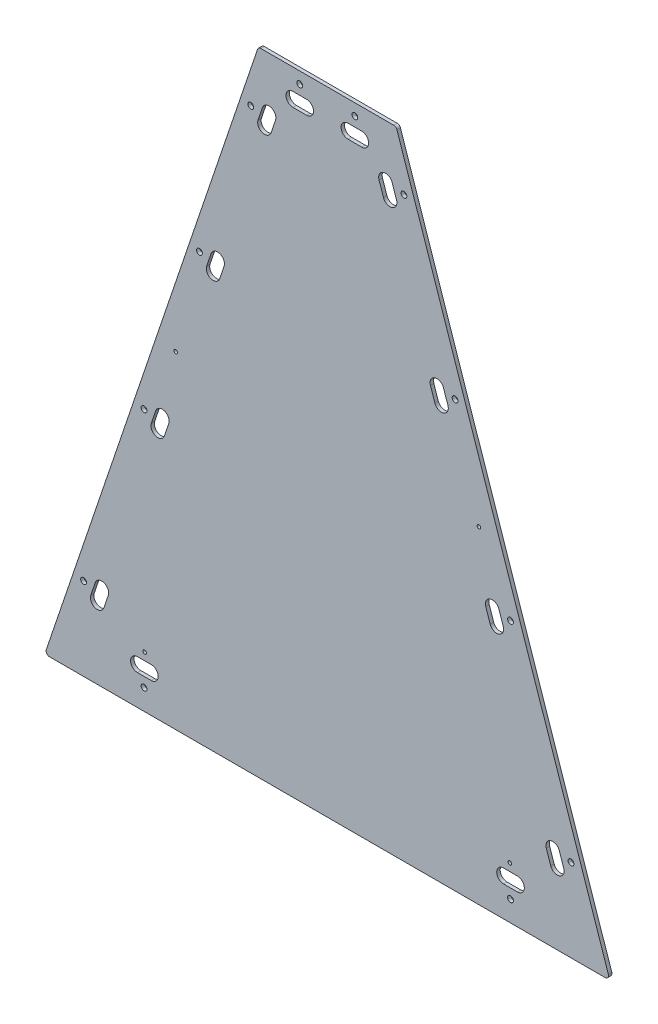
SolidWorks part; units mm, degrees
material "PC High Viscosity"
ref_plane "Front Plane" through (0, 0, 0) normal (0, 0, 1) x (1, 0, 0)
ref_plane "Top Plane" through (0, 0, 0) normal (0, 1, 0) x (1, 0, 0)
ref_plane "Right Plane" through (0, 0, 0) normal (1, 0, 0) x (0, 0, -1)
sketch "Sketch1" plane through (0, 0, 0) normal (0, 0, 1) x (1, 0, 0)
  line L0 (128.5466, 292.9716) -> (382.5466, 292.9716)
  line L5 (382.5466, 292.9716) -> (776.2466, -872.6346)
  line L6 (776.2466, -872.6346) -> (-265.1534, -872.6346)
  line L7 (-265.1534, -872.6346) -> (128.5466, 292.9716)
  line L8 (-168.2075, -740.392) -> (-160.0795, -716.3277) construction
  line L9 (-180.2397, -736.328) -> (-172.1116, -712.2636)
  line L10 (-156.1753, -744.4561) -> (-148.0473, -720.3917)
  line L11 (-94.2317, -804.0546) -> (-68.8317, -804.0546) construction
  line L12 (-94.2317, -791.3546) -> (-68.8317, -791.3546)
  line L13 (-94.2317, -816.7546) -> (-68.8317, -816.7546)
  line L14 (580.5201, -804.0546) -> (605.9201, -804.0546) construction
  line L15 (580.5201, -791.3546) -> (605.9201, -791.3546)
  line L16 (580.5201, -816.7546) -> (605.9201, -816.7546)
  line L17 (-56.7399, -410.3759) -> (-48.6118, -386.3115) construction
  line L18 (-68.7721, -406.3118) -> (-60.644, -382.2474)
  line L19 (-44.7077, -414.4399) -> (-36.5796, -390.3755)
  line L20 (45.2346, -108.4656) -> (53.3626, -84.4012) construction
  line L21 (33.2024, -104.4015) -> (41.3305, -80.3372)
  line L22 (57.2668, -112.5296) -> (65.3948, -88.4652)
  line L29 (139.9814, 172.0464) -> (148.1095, 196.1108) construction
  line L30 (127.9493, 176.1104) -> (136.0773, 200.1748)
  line L31 (152.0136, 167.9823) -> (160.1417, 192.0467)
  line L32 (192.1135, 241.2472) -> (217.5135, 241.2472) construction
  line L33 (192.1135, 253.9472) -> (217.5135, 253.9472)
  line L34 (192.1135, 228.5472) -> (217.5135, 228.5472)
  line L35 (293.6466, 241.2472) -> (319.0466, 241.2472) construction
  line L36 (293.6466, 253.9472) -> (319.0466, 253.9472)
  line L37 (293.6466, 228.5472) -> (319.0466, 228.5472)
  line L38 (371.0972, 172.0897) -> (362.9691, 196.154) construction
  line L39 (359.065, 168.0256) -> (350.9369, 192.09)
  line L40 (383.1294, 176.1537) -> (375.0013, 200.2181)
  line L41 (465.8587, -108.4656) -> (457.7306, -84.4012) construction
  line L42 (453.8265, -112.5296) -> (445.6984, -88.4652)
  line L43 (477.8909, -104.4015) -> (469.7628, -80.3372)
  line L44 (679.3008, -740.392) -> (671.1727, -716.3277) construction
  line L47 (567.8332, -410.3759) -> (559.7051, -386.3115) construction
  line L48 (555.801, -414.4399) -> (547.6729, -390.3755)
  line L49 (579.8654, -406.3118) -> (571.7373, -382.2474)
  line L50 (667.2686, -744.4561) -> (659.1405, -720.3917)
  line L53 (691.333, -736.328) -> (683.2049, -712.2636)
  circle A0 centre (396.7562, 191.3716) radius 5.3578
  circle A1 centre (114.6592, 192.3252) radius 5.3578
  circle A2 centre (-193.5708, -720.2346) radius 5.3578
  circle A4 centre (704.6641, -720.2346) radius 5.3578
  circle A5 centre (491.1275, -88.0284) radius 5.3578
  circle A6 centre (593.2201, -390.2884) radius 5.3578
  circle A7 centre (19.9658, -88.0284) radius 5.3578
  circle A8 centre (-82.1268, -390.2884) radius 5.3578
  circle A9 centre (306.3466, 271.7272) radius 5.3578
  circle A10 centre (204.7466, 271.7272) radius 5.3578
  circle A12 centre (-82.1268, -834.5346) radius 5.3578
  circle A13 centre (593.2201, -834.5346) radius 5.3578
  arc A14 (-180.2397, -736.328) -> (-156.1753, -744.4561) centre (-168.2075, -740.392) ccw
  arc A15 (-148.0473, -720.3917) -> (-172.1116, -712.2636) centre (-160.0795, -716.3277) ccw
  arc A16 (-94.2317, -791.3546) -> (-94.2317, -816.7546) centre (-94.2317, -804.0546) ccw
  arc A17 (-68.8317, -816.7546) -> (-68.8317, -791.3546) centre (-68.8317, -804.0546) ccw
  arc A18 (580.5201, -791.3546) -> (580.5201, -816.7546) centre (580.5201, -804.0546) ccw
  arc A19 (605.9201, -816.7546) -> (605.9201, -791.3546) centre (605.9201, -804.0546) ccw
  arc A20 (-68.7721, -406.3118) -> (-44.7077, -414.4399) centre (-56.7399, -410.3759) ccw
  arc A21 (-36.5796, -390.3755) -> (-60.644, -382.2474) centre (-48.6118, -386.3115) ccw
  arc A22 (33.2024, -104.4015) -> (57.2668, -112.5296) centre (45.2346, -108.4656) ccw
  arc A23 (65.3948, -88.4652) -> (41.3305, -80.3372) centre (53.3626, -84.4012) ccw
  arc A28 (127.9493, 176.1104) -> (152.0136, 167.9823) centre (139.9814, 172.0464) ccw
  arc A29 (160.1417, 192.0467) -> (136.0773, 200.1748) centre (148.1095, 196.1108) ccw
  arc A30 (192.1135, 253.9472) -> (192.1135, 228.5472) centre (192.1135, 241.2472) ccw
  arc A31 (217.5135, 228.5472) -> (217.5135, 253.9472) centre (217.5135, 241.2472) ccw
  arc A32 (293.6466, 253.9472) -> (293.6466, 228.5472) centre (293.6466, 241.2472) ccw
  arc A33 (319.0466, 228.5472) -> (319.0466, 253.9472) centre (319.0466, 241.2472) ccw
  arc A34 (359.065, 168.0256) -> (383.1294, 176.1537) centre (371.0972, 172.0897) ccw
  arc A35 (375.0013, 200.2181) -> (350.9369, 192.09) centre (362.9691, 196.154) ccw
  arc A36 (453.8265, -112.5296) -> (477.8909, -104.4015) centre (465.8587, -108.4656) ccw
  arc A37 (469.7628, -80.3372) -> (445.6984, -88.4652) centre (457.7306, -84.4012) ccw
  arc A40 (555.801, -414.4399) -> (579.8654, -406.3118) centre (567.8332, -410.3759) ccw
  arc A41 (571.7373, -382.2474) -> (547.6729, -390.3755) centre (559.7051, -386.3115) ccw
  arc A44 (667.2686, -744.4561) -> (691.333, -736.328) centre (679.3008, -740.392) ccw
  arc A45 (683.2049, -712.2636) -> (659.1405, -720.3917) centre (671.1727, -716.3277) ccw
  point P24 (-164.1435, -728.3598)
  point P39 (-81.5317, -804.0546)
  point P47 (593.2201, -804.0546)
  point P56 (-52.6759, -398.3437)
  point P62 (204.8135, 241.2472)
  point P65 (49.2986, -96.4334)
  point P93 (144.0455, 184.0786)
  point P106 (306.3466, 241.2472)
  point P115 (367.0332, 184.1219)
  point P125 (461.7947, -96.4334)
  point P136 (675.2368, -728.3598)
  point P140 (563.7691, -398.3437)
  dimension "D5" = 10.7156
  dimension "D6" = 19.05
  dimension "D7" = 17.78
  dimension "D8" = 17.78
  dimension "D9" = 17.78
  dimension "D10" = 17.78
  dimension "D11" = 17.78
  dimension "D12" = 17.78
  dimension "D13" = 38.1
  dimension "D31" = 183.6216
  dimension "D32" = 144.2748
  dimension "D36" = 108.893
  dimension "D37" = 17.78
  dimension "D41" = 76.2669
  dimension "D34" = 776.2012
  dimension "D35" = 25.4
  dimension "D1" = 254
  dimension "D2" = 1230.2998
  dimension "D3" = 1230.2998
  dimension "D4" = 1041.4
  dimension "D14" = 19.05
  dimension "D15" = 683.26
  dimension "D16" = 19.05
  dimension "D17" = 76.2
  dimension "D18" = 381
  dimension "D19" = 683.26
  dimension "D20" = 152.4
  dimension "D21" = 152.4
  dimension "D22" = 19.05
  dimension "D23" = 76.2
  dimension "D24" = 19.05
  dimension "D25" = 381
  dimension "D26" = 101.6
  dimension "D27" = 19.05
  dimension "D28" = 19.05
  dimension "D29" = 19.05
  dimension "D30" = 101.6
  dimension "D33" = 474.291
  dimension "D38" = 38.1
  dimension "D39" = 25.4
  dimension "D40" = 17.78
  dimension "D42" = 17.78
  dimension "D43" = 108.8497
  dimension "D47" = 17.78
  dimension "D52" = 17.78
  dimension "D53" = 17.78
  dimension "D56" = 21.2444
  dimension "D57" = 21.2444
extrude "Boss-Extrude1" add sketch "Sketch1" along normal blind 6.35 contours L7 L6 L5 L0 A29 L31 A28 L30 A23 L22 A22 L21 A21 L19 A20 L18 A19 L16 A18 L15 A17 L13 A16 L12 A15 L10 A14 L9 A13 A12 A10 A9 A8 A7 A6 A5
fillet "Fillet1" radius 6.35 4 edges at (-265.1534, -872.6346, 3.175) (776.2466, -872.6346, 3.175) (382.5466, 292.9716, 3.175) (128.5466, 292.9716, 3.175)
sketch "Sketch2" plane through (0, 0, 6.35) normal (0, 0, 1) x (1, 0, 0)
  line L0 (255.5466, -872.6346) -> (255.5466, 292.9716) construction
  line L1 (767.3994, -872.6346) -> (-256.3061, -872.6346) construction
  line L2 (133.1043, 292.9716) -> (377.989, 292.9716) construction
  line L3 (91.6472, -808.2573) -> (67.9728, -842.0678)
  line L4 (443.1205, -842.0678) -> (419.4461, -808.2573)
  arc A0 (91.6472, -808.2573) -> (419.4461, -808.2573) centre (255.5466, -574.1846) cw
  arc A1 (67.9728, -842.0678) -> (443.1205, -842.0678) centre (255.5466, -574.1846) cw
  point P0 (255.5466, -288.4346)
  dimension "D3" = 298.45
  dimension "D1" = 41.275
  dimension "D2" = 584.2
  dimension "D4" = 70
sketch "Sketch4" [suppressed] plane through (0, 0, 6.35) normal (0, 0, 1) x (1, 0, 0)
  line L0 (414.1087, -288.4346) -> (255.5466, -288.4346)
  line L13 (414.1087, -288.4346) -> (572.6707, -563.0721)
  line L14 (572.6707, -563.0721) -> (414.1087, -837.7096)
  line L15 (767.3994, -872.6346) -> (-256.3061, -872.6346) construction
  line L16 (255.5466, -288.4346) -> (255.5466, -872.6346) construction
  line L17 (437.9388, -247.1596) -> (255.5466, -247.1596)
  line L18 (437.9388, -247.1596) -> (620.331, -563.0721)
  line L19 (620.331, -563.0721) -> (449.8539, -858.3471)
  line L20 (449.8539, -858.3471) -> (414.1087, -837.7096)
  line L21 (61.2394, -858.3471) -> (96.9846, -837.7096)
  line L22 (-109.2377, -563.0721) -> (61.2394, -858.3471)
  line L23 (73.1545, -247.1596) -> (-109.2377, -563.0721)
  line L24 (73.1545, -247.1596) -> (255.5466, -247.1596)
  line L25 (-61.5774, -563.0721) -> (96.9846, -837.7096)
  line L26 (96.9846, -288.4346) -> (-61.5774, -563.0721)
  line L27 (96.9846, -288.4346) -> (255.5466, -288.4346)
  line L28 (414.1087, -837.7096) -> (96.9846, -837.7096) construction
  dimension "D1" = 309.5625
  dimension "D2" = 317.1241
  dimension "D3" = 120
  dimension "D4" = 120
  dimension "D5" = 41.275
extrude "Cut-Extrude1" [suppressed] cut sketch "Sketch2" against normal through all
extrude "Cut-Extrude2" [suppressed] cut sketch "Sketch4" against normal through all
sketch "Sketch5" [suppressed] plane through (0, 0, 6.35) normal (0, 0, 1) x (1, 0, 0)
  line L0 (57.2668, -112.5296) -> (65.3948, -88.4652) construction
  line L1 (33.2024, -104.4015) -> (41.3305, -80.3372) construction
  line L2 (-44.7077, -414.4399) -> (-36.5796, -390.3755) construction
  line L3 (-68.7721, -406.3118) -> (-60.644, -382.2474) construction
  line L4 (-180.2397, -736.328) -> (-172.1116, -712.2636) construction
  line L5 (-156.1753, -744.4561) -> (-148.0473, -720.3917) construction
  line L6 (-94.2317, -816.7546) -> (-68.8317, -816.7546) construction
  line L7 (-94.2317, -791.3546) -> (-68.8317, -791.3546) construction
  line L8 (57.2668, -112.5296) -> (65.3948, -88.4652)
  line L9 (33.2024, -104.4015) -> (41.3305, -80.3372)
  line L10 (-44.7077, -414.4399) -> (-36.5796, -390.3755)
  line L11 (-68.7721, -406.3118) -> (-60.644, -382.2474)
  line L12 (-180.2397, -736.328) -> (-172.1116, -712.2636)
  line L13 (-156.1753, -744.4561) -> (-148.0473, -720.3917)
  line L14 (-94.2317, -816.7546) -> (-68.8317, -816.7546)
  line L15 (-94.2317, -791.3546) -> (-68.8317, -791.3546)
  line L16 (192.1135, 228.5472) -> (217.5135, 228.5472) construction
  line L17 (192.1135, 253.9472) -> (217.5135, 253.9472) construction
  line L18 (152.0136, 167.9823) -> (160.1417, 192.0467) construction
  line L19 (127.9493, 176.1104) -> (136.0773, 200.1748) construction
  line L20 (192.1135, 228.5472) -> (217.5135, 228.5472)
  line L21 (192.1135, 253.9472) -> (217.5135, 253.9472)
  line L22 (152.0136, 167.9823) -> (160.1417, 192.0467)
  line L23 (127.9493, 176.1104) -> (136.0773, 200.1748)
  line L24 (255.5466, 292.9716) -> (255.5466, -872.6346) construction
  line L37 (359.065, 168.0256) -> (350.9369, 192.09) construction
  line L38 (383.1294, 176.1537) -> (375.0013, 200.2181) construction
  line L39 (293.6466, 228.5472) -> (319.0466, 228.5472) construction
  line L40 (293.6466, 253.9472) -> (319.0466, 253.9472) construction
  line L41 (359.065, 168.0256) -> (350.9369, 192.09)
  line L42 (383.1294, 176.1537) -> (375.0013, 200.2181)
  line L43 (293.6466, 228.5472) -> (319.0466, 228.5472)
  line L44 (293.6466, 253.9472) -> (319.0466, 253.9472)
  line L45 (453.8265, -112.5296) -> (445.6984, -88.4652) construction
  line L46 (477.8909, -104.4015) -> (469.7628, -80.3372) construction
  line L47 (453.8265, -112.5296) -> (445.6984, -88.4652)
  line L48 (477.8909, -104.4015) -> (469.7628, -80.3372)
  line L49 (555.801, -414.4399) -> (547.6729, -390.3755) construction
  line L50 (579.8654, -406.3118) -> (571.7373, -382.2474) construction
  line L51 (555.801, -414.4399) -> (547.6729, -390.3755)
  line L52 (579.8654, -406.3118) -> (571.7373, -382.2474)
  line L53 (667.2686, -744.4561) -> (659.1405, -720.3917) construction
  line L54 (691.333, -736.328) -> (683.2049, -712.2636) construction
  line L55 (667.2686, -744.4561) -> (659.1405, -720.3917)
  line L56 (691.333, -736.328) -> (683.2049, -712.2636)
  line L57 (580.5201, -791.3546) -> (605.9201, -791.3546) construction
  line L58 (580.5201, -816.7546) -> (605.9201, -816.7546) construction
  line L59 (580.5201, -791.3546) -> (605.9201, -791.3546)
  line L60 (580.5201, -816.7546) -> (605.9201, -816.7546)
  arc A0 (33.2024, -104.4015) -> (57.2668, -112.5296) centre (45.2346, -108.4656) ccw construction
  arc A1 (65.3948, -88.4652) -> (41.3305, -80.3372) centre (53.3626, -84.4012) ccw construction
  circle A2 centre (19.9658, -88.0284) radius 5.3578 construction
  arc A3 (-68.7721, -406.3118) -> (-44.7077, -414.4399) centre (-56.7399, -410.3759) ccw construction
  circle A4 centre (-82.1268, -390.2884) radius 5.3578 construction
  arc A5 (-36.5796, -390.3755) -> (-60.644, -382.2474) centre (-48.6118, -386.3115) ccw construction
  circle A6 centre (-193.5708, -720.2346) radius 5.3578 construction
  arc A7 (-148.0473, -720.3917) -> (-172.1116, -712.2636) centre (-160.0795, -716.3277) ccw construction
  arc A8 (-180.2397, -736.328) -> (-156.1753, -744.4561) centre (-168.2075, -740.392) ccw construction
  arc A9 (-94.2317, -791.3546) -> (-94.2317, -816.7546) centre (-94.2317, -804.0546) ccw construction
  arc A10 (-68.8317, -816.7546) -> (-68.8317, -791.3546) centre (-68.8317, -804.0546) ccw construction
  circle A11 centre (-82.1268, -834.5346) radius 5.3578 construction
  arc A12 (33.2024, -104.4015) -> (57.2668, -112.5296) centre (45.2346, -108.4656) ccw
  arc A13 (65.3948, -88.4652) -> (41.3305, -80.3372) centre (53.3626, -84.4012) ccw
  circle A14 centre (19.9658, -88.0284) radius 5.3578
  arc A15 (-68.7721, -406.3118) -> (-44.7077, -414.4399) centre (-56.7399, -410.3759) ccw
  circle A16 centre (-82.1268, -390.2884) radius 5.3578
  arc A17 (-36.5796, -390.3755) -> (-60.644, -382.2474) centre (-48.6118, -386.3115) ccw
  circle A18 centre (-193.5708, -720.2346) radius 5.3578
  arc A19 (-148.0473, -720.3917) -> (-172.1116, -712.2636) centre (-160.0795, -716.3277) ccw
  arc A20 (-180.2397, -736.328) -> (-156.1753, -744.4561) centre (-168.2075, -740.392) ccw
  arc A21 (-94.2317, -791.3546) -> (-94.2317, -816.7546) centre (-94.2317, -804.0546) ccw
  arc A22 (-68.8317, -816.7546) -> (-68.8317, -791.3546) centre (-68.8317, -804.0546) ccw
  circle A23 centre (-82.1268, -834.5346) radius 5.3578
  arc A24 (217.5135, 228.5472) -> (217.5135, 253.9472) centre (217.5135, 241.2472) ccw construction
  arc A25 (192.1135, 253.9472) -> (192.1135, 228.5472) centre (192.1135, 241.2472) ccw construction
  circle A26 centre (204.7466, 271.7272) radius 5.3578 construction
  arc A27 (127.9493, 176.1104) -> (152.0136, 167.9823) centre (139.9814, 172.0464) ccw construction
  arc A28 (160.1417, 192.0467) -> (136.0773, 200.1748) centre (148.1095, 196.1108) ccw construction
  circle A29 centre (114.6592, 192.3252) radius 5.3578 construction
  arc A30 (217.5135, 228.5472) -> (217.5135, 253.9472) centre (217.5135, 241.2472) ccw
  arc A31 (192.1135, 253.9472) -> (192.1135, 228.5472) centre (192.1135, 241.2472) ccw
  circle A32 centre (204.7466, 271.7272) radius 5.3578
  arc A33 (127.9493, 176.1104) -> (152.0136, 167.9823) centre (139.9814, 172.0464) ccw
  arc A34 (160.1417, 192.0467) -> (136.0773, 200.1748) centre (148.1095, 196.1108) ccw
  circle A35 centre (114.6592, 192.3252) radius 5.3578
  circle A54 centre (306.3466, 271.7272) radius 5.3578 construction
  circle A55 centre (306.3466, 271.7272) radius 5.3578
  circle A56 centre (396.7562, 191.3716) radius 5.3578 construction
  arc A57 (359.065, 168.0256) -> (383.1294, 176.1537) centre (371.0972, 172.0897) ccw construction
  arc A58 (375.0013, 200.2181) -> (350.9369, 192.09) centre (362.9691, 196.154) ccw construction
  arc A59 (293.6466, 253.9472) -> (293.6466, 228.5472) centre (293.6466, 241.2472) ccw construction
  arc A60 (319.0466, 228.5472) -> (319.0466, 253.9472) centre (319.0466, 241.2472) ccw construction
  circle A61 centre (396.7562, 191.3716) radius 5.3578
  arc A62 (359.065, 168.0256) -> (383.1294, 176.1537) centre (371.0972, 172.0897) ccw
  arc A63 (375.0013, 200.2181) -> (350.9369, 192.09) centre (362.9691, 196.154) ccw
  arc A64 (293.6466, 253.9472) -> (293.6466, 228.5472) centre (293.6466, 241.2472) ccw
  arc A65 (319.0466, 228.5472) -> (319.0466, 253.9472) centre (319.0466, 241.2472) ccw
  arc A66 (453.8265, -112.5296) -> (477.8909, -104.4015) centre (465.8587, -108.4656) ccw construction
  arc A67 (469.7628, -80.3372) -> (445.6984, -88.4652) centre (457.7306, -84.4012) ccw construction
  circle A68 centre (491.1275, -88.0284) radius 5.3578 construction
  arc A69 (453.8265, -112.5296) -> (477.8909, -104.4015) centre (465.8587, -108.4656) ccw
  arc A70 (469.7628, -80.3372) -> (445.6984, -88.4652) centre (457.7306, -84.4012) ccw
  circle A71 centre (491.1275, -88.0284) radius 5.3578
  arc A72 (555.801, -414.4399) -> (579.8654, -406.3118) centre (567.8332, -410.3759) ccw construction
  circle A73 centre (593.2201, -390.2884) radius 5.3578 construction
  arc A74 (571.7373, -382.2474) -> (547.6729, -390.3755) centre (559.7051, -386.3115) ccw construction
  arc A75 (555.801, -414.4399) -> (579.8654, -406.3118) centre (567.8332, -410.3759) ccw
  circle A76 centre (593.2201, -390.2884) radius 5.3578
  arc A77 (571.7373, -382.2474) -> (547.6729, -390.3755) centre (559.7051, -386.3115) ccw
  arc A78 (667.2686, -744.4561) -> (691.333, -736.328) centre (679.3008, -740.392) ccw construction
  arc A79 (683.2049, -712.2636) -> (659.1405, -720.3917) centre (671.1727, -716.3277) ccw construction
  circle A80 centre (704.6641, -720.2346) radius 5.3578 construction
  arc A81 (667.2686, -744.4561) -> (691.333, -736.328) centre (679.3008, -740.392) ccw
  arc A82 (683.2049, -712.2636) -> (659.1405, -720.3917) centre (671.1727, -716.3277) ccw
  circle A83 centre (704.6641, -720.2346) radius 5.3578
  arc A84 (605.9201, -816.7546) -> (605.9201, -791.3546) centre (605.9201, -804.0546) ccw construction
  circle A85 centre (593.2201, -834.5346) radius 5.3578 construction
  arc A86 (580.5201, -791.3546) -> (580.5201, -816.7546) centre (580.5201, -804.0546) ccw construction
  arc A87 (605.9201, -816.7546) -> (605.9201, -791.3546) centre (605.9201, -804.0546) ccw
  circle A88 centre (593.2201, -834.5346) radius 5.3578
  arc A89 (580.5201, -791.3546) -> (580.5201, -816.7546) centre (580.5201, -804.0546) ccw
extrude "Boss-Extrude2" [suppressed] add sketch "Sketch5" against normal up to surface (6.35 mm away)
sketch "Sketch6" plane through (0, 0, 6.35) normal (0, 0, 1) x (1, 0, 0)
  line L0 (255.5466, 292.9716) -> (255.5466, -872.6346) construction
  line L1 (133.1043, 292.9716) -> (377.989, 292.9716) construction
  line L2 (767.3994, -872.6346) -> (-256.3061, -872.6346) construction
  point P0 (-81.0034, -777.3846)
  point P1 (-23.8534, -269.3846)
  point P2 (534.9466, -269.3846)
  point P3 (592.0966, -777.3846)
  dimension "D1" = 673.1
  dimension "D2" = 336.55
  dimension "D3" = 558.8
  dimension "D4" = 279.4
  dimension "D5" = 508
  dimension "D6" = 95.25
hole_wizard "17/64 (0.26563) Diameter Hole1" positions "Sketch7" profile "Sketch8" hole size "17/64" standard "ANSI Inch" end condition through all
sketch "Sketch7" plane through (0, 0, 6.35) normal (0, 0, 1) x (1, 0, 0)
  point P0 (-23.8534, -269.3846)
  point P3 (534.9466, -269.3846)
  point P6 (592.0966, -777.3846)
  point P9 (-81.0034, -777.3846)
sketch "Sketch8" plane through (-23.8534, -269.3846, 6.35) normal (1, 0, 0) x (0, -1, 0)
  line L0 (0, 0) -> (0, 6.35)
  line L1 (0, 6.35) -> (3.3735, 6.35)
  line L2 (3.3735, 6.35) -> (3.3735, 0)
  line L5 (3.3735, 0) -> (0, 0)
  line L11 (0, -6.35) -> (0, 107.95) construction
  dimension "Thru Hole Dia." = 6.747
  dimension "Thru Hole Depth" = 6.35
equation "\"D2@Sketch6\"=\"D1@Sketch6\"/2"
equation "\"D4@Sketch6\"=\"D3@Sketch6\"/2"
